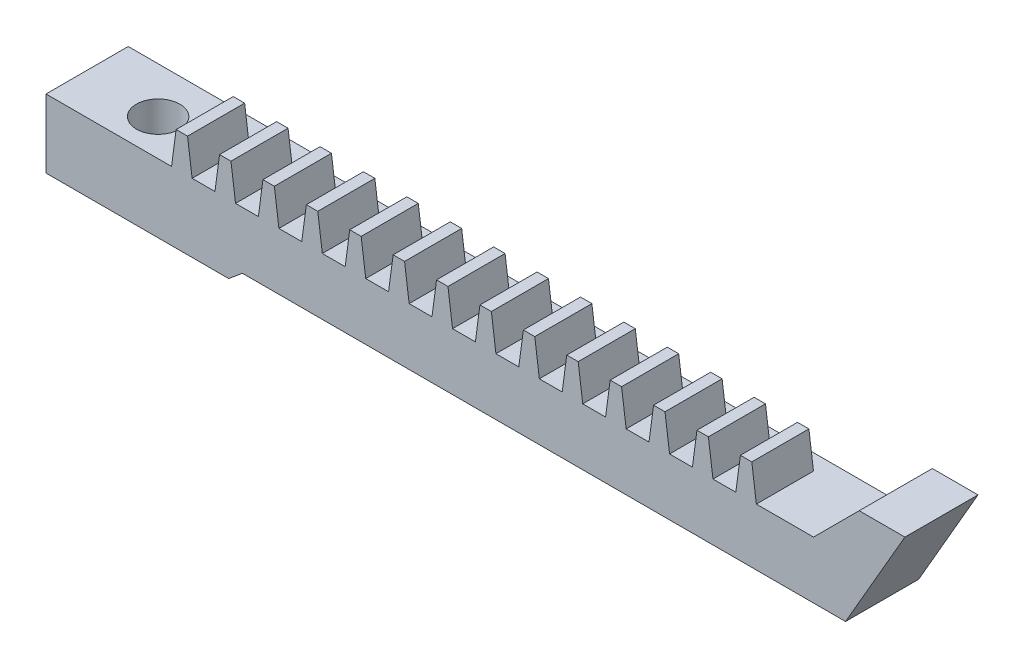
SolidWorks part; units mm, degrees
material "uhlíková ocel 7850"
ref_plane "Přední rovina" through (0, 0, 0) normal (0, 0, 1) x (1, 0, 0)
ref_plane "Horní rovina" through (0, 0, 0) normal (0, 1, 0) x (1, 0, 0)
ref_plane "Pravá rovina" through (0, 0, 0) normal (1, 0, 0) x (0, 0, -1)
sketch "Skica1" plane through (0, 0, 0) normal (0, 0, 1) x (1, 0, 0)
  line L0 (0, 0) -> (0, -3)
  line L1 (0, -3) -> (8, -3)
  line L2 (8, -3) -> (8.5959, -2.5)
  line L3 (8.5959, -2.5) -> (35, -2.5)
  line L4 (35, -2.5) -> (37.5981, 2)
  line L5 (37.5981, 2) -> (35.5981, 2)
  line L6 (35.5981, 2) -> (33.5981, 0)
  line L7 (33.5981, 0) -> (0, 0)
  dimension "D1" = 8
  dimension "D2" = 3
  dimension "D3" = 35
  dimension "D4" = 0.5
  dimension "D5" = 140
  dimension "D6" = 60
  dimension "D7" = 2
  dimension "D8" = 4.5
  dimension "D9" = 15
extrude "Přidat vysunutím1" add sketch "Skica1" along normal blind 3.6
sketch "Skica2" plane through (0, 0, 0) normal (0, 1, 0) x (1, 0, 0)
  line L0 (8, 0) -> (8.5959, -0.4)
  line L1 (8.5959, -3.6) -> (8.5959, 0) construction
  line L2 (8.5959, -0.4) -> (37.5981, -0.4)
  line L3 (37.5981, -3.6) -> (37.5981, 0) construction
  line L4 (37.5981, -0.4) -> (37.5981, 0)
  line L5 (37.5981, 0) -> (8, 0)
  dimension "D1" = 0.4
extrude "Odebrat vysunutím1" cut sketch "Skica2" against normal through all both and the other way through all
sketch "Skica3" plane through (0, -4.2, 3.6) normal (0, 0, -1) x (1, 0, 0)
  line L0 (9.2959, -4.2) -> (10.1959, -4.2)
  line L1 (33.5981, -4.2) -> (8.5959, -4.2) construction
  line L2 (10.1959, -4.2) -> (9.9959, -5.7)
  line L3 (9.9959, -5.7) -> (9.4959, -5.7)
  line L4 (9.4959, -5.7) -> (9.2959, -4.2)
  dimension "D1" = 0.9
  dimension "D2" = 1.5
  dimension "D3" = 0.5
  dimension "D4" = 0.7
extrude "Přidat vysunutím2" add sketch "Skica3" along normal blind 2.5
pattern_linear "LinPole1" count 12 spacing 1.9 along (1, 0, 0) count 3 spacing 1.9 along (-1, 0, 0) of "Přidat vysunutím2"
sketch "Skica4" plane through (0, 0, 3.6) normal (0, 0, 1) x (1, 0, 0)
  line L0 (-2.9354, -3) -> (6.0646, -3) construction
  line L1 (0, 0) -> (0, -3) construction
  circle A0 centre (3, -1.5) radius 1
  dimension "D1" = 2
  dimension "D2" = 1.5
  dimension "D3" = 3
sketch "Skica5" plane through (0, -3, 0) normal (0, -1, 0) x (1, 0, 0)
  line L0 (4.4146, 2.0061) -> (2.2146, 2.0061) construction
  circle A0 centre (3.3146, 2.0061) radius 0.95
  dimension "D1" = 1.9
extrude "Odebrat vysunutím2" cut sketch "Skica5" against normal blind 5
